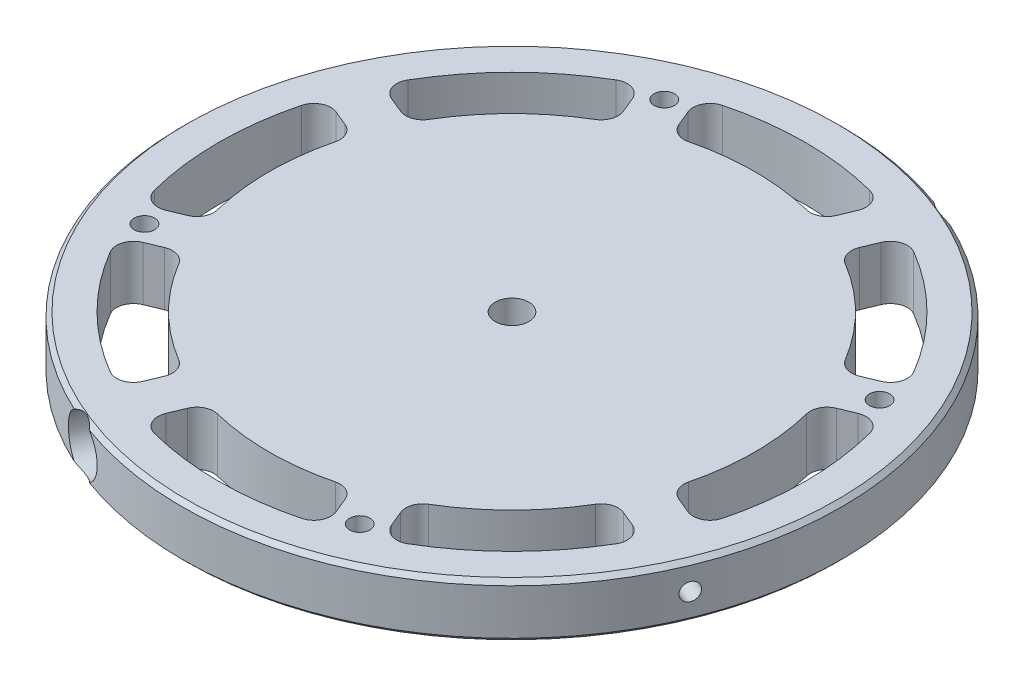
SolidWorks part; units mm, degrees
material "6061-T6 (SS)"
ref_plane "Front Plane" through (0, 0, 0) normal (0, 0, 1) x (1, 0, 0)
ref_plane "Top Plane" through (0, 0, 0) normal (0, 1, 0) x (1, 0, 0)
ref_plane "Right Plane" through (0, 0, 0) normal (1, 0, 0) x (0, 0, -1)
sketch "Sketch2" plane through (0, 0, 0) normal (1, 0, 0) x (0, 0, -1)
  line L0 (0, 0) -> (-77.55, 0)
  line L1 (-77.55, 0) -> (-77.55, 12.7)
  line L2 (-77.55, 12.7) -> (0, 12.7)
  line L5 (0, 12.7) -> (0, 0)
  dimension "D1" = 77.55
  dimension "D2" = 12.7
ref_axis "Axis1" through (0, -0.8888, 0) along (0, 1, 0)
revolve "Revolve1" add sketch "Sketch2" angle 360 about axis through (0, -0.8888, 0) along (0, 1, 0)
hole_wizard "#12 (0.189) Diameter Hole1" positions "Sketch6" profile "Sketch7" hole size "#12" standard "ANSI Inch" end condition through all
sketch "Sketch6" plane through (0, 12.7, 0) normal (0, 1, 0) x (1, 0, 0)
  line L0 (0, 0) -> (-53.438, 129.0108) construction
  line L2 (0, 0) -> (0, 109.0908) construction
  point P0 (-25.3336, 61.1608)
  dimension "D1" = 22.5
  dimension "D2" = 66.2
sketch "Sketch7" plane through (-25.3336, 12.7, -61.1608) normal (1, 0, 0) x (0, 0, 1)
  line L0 (0, 0) -> (0, 12.7)
  line L1 (0, 12.7) -> (2.4003, 12.7)
  line L2 (2.4003, 12.7) -> (2.4003, 0)
  line L5 (2.4003, 0) -> (0, 0)
  line L11 (0, -6.35) -> (0, 107.95) construction
  dimension "Thru Hole Dia." = 4.8006
  dimension "Thru Hole Depth" = 12.7
pattern_circular "CirPattern3" count 4 over 360 about axis through (0, 0, 0) along (0, 1, 0) of "#12 (0.189) Diameter Hole1"
sketch "Sketch8" plane through (0, 12.7, 0) normal (0, 1, 0) x (1, 0, 0)
  line L4 (0, 0) -> (0, 93.9995) construction
  line L5 (0, 0) -> (113.8372, 0) construction
  line L6 (-17.1671, 54.5107) -> (-21.7355, 65.5398)
  line L7 (17.1671, 54.5107) -> (21.7355, 65.5398)
  line L8 (0, 0) -> (-25.3336, 61.1608) construction
  arc A0 (-17.1671, 54.5107) -> (17.1671, 54.5107) centre (0, 0) cw
  arc A1 (-21.7355, 65.5398) -> (21.7355, 65.5398) centre (0, 0) cw
  circle A2 centre (0, 0) radius 77.55 construction
  dimension "D1" = 57.15
  dimension "D2" = 8.5
  dimension "D3" = 5
extrude "Cut-Extrude1" cut sketch "Sketch8" against normal through all
fillet "Fillet1" radius 4 4 edges at (17.1671, 6.35, -54.5107) (21.7355, 6.35, -65.5398) (-17.1671, 6.35, -54.5107) (-21.7355, 6.35, -65.5398)
pattern_circular "CirPattern4" count 8 over 360 about axis through (0, 0, 0) along (0, 1, 0) of "Cut-Extrude1", "Fillet1"
chamfer "Chamfer1" distance 1 angle 45 2 edges at (0, 0, -77.55) (0, 12.7, -77.55)
ref_plane "Plane1" through (0, 0, 0) normal (0.9239, 0, 0.3827) x (0, 1, 0)
hole_wizard "#20 (0.161) Diameter Hole1" positions "Sketch16" profile "Sketch15" hole size "#20" standard "ANSI Inch"
sketch "Sketch16" plane through (0, 0, 0) normal (0.9239, 0, 0.3827) x (0, 1, 0)
  point P0 (6.35, 0)
  dimension "D1" = 6.35
sketch "Sketch15" plane through (0, 6.35, 0) normal (0, 1, 0) x (-0.3827, 0, 0.9239)
  line L0 (0, 0) -> (0, 101.324)
  line L1 (0, 101.324) -> (2.0447, 101.324)
  line L2 (2.0447, 101.324) -> (2.0447, 0)
  line L5 (2.0447, 0) -> (0, 0)
  line L11 (0, -6.35) -> (0, 107.95) construction
  dimension "Thru Hole Dia." = 4.0894
  dimension "Thru Hole Depth" = 101.324
ref_plane "Plane2" through (29.6771, 0, -71.6469) normal (0.3827, 0, -0.9239) x (-0.9239, 0, -0.3827)
sketch "Sketch19" plane through (29.6771, 0, -71.6469) normal (0.3827, 0, -0.9239) x (-0.9239, 0, -0.3827)
  line L0 (-76.55, 0) -> (76.55, 0) construction
  line L2 (0, -0.8888) -> (0, 13.5888) construction
  circle A0 centre (0, 6.35) radius 5.5625 construction
  circle A1 centre (0, 6.35) radius 6.25
  dimension "D1" = 12.5
  dimension "D2" = 6.35
extrude "Cut-Extrude3" cut sketch "Sketch19" against normal blind 5
pattern_circular "CirPattern5" count 2 over 360 about axis through (0, -0.8888, 0) along (0, 1, 0) of "Cut-Extrude3"
hole_wizard "#10-24 Tapped Hole1" positions "Sketch20" profile "Sketch21" tap size "#10-24" standard "ANSI Inch"
sketch "Sketch20" plane through (-27.7637, 0, 67.0275) normal (-0.3827, 0, 0.9239) x (0.9239, 0, 0.3827)
  circle A0 centre (0, 6.35) radius 6.25
  circle A1 centre (0, 6.35) radius 6.25 construction
  point P0 (0, 6.35)
sketch "Sketch21" plane through (-27.7637, 6.35, 67.0275) normal (0, 1, 0) x (0.9239, 0, 0.3827)
  line L0 (0, 0) -> (0, 51.9408)
  line L1 (0, 51.9408) -> (1.8986, 50.8)
  line L2 (1.8986, 50.8) -> (1.8986, 0)
  line L5 (1.8986, 0) -> (0, 0)
  line L10 (0, 51.9408) -> (-1.8986, 50.8) construction
  line L11 (0, -6.35) -> (0, 107.95) construction
  dimension "Tap Drill Dia." = 3.7973
  dimension "Tap Drill Depth" = 50.8
  dimension "Drill Angle" = 118
pattern_circular "CirPattern6" count 2 over 360 about axis through (0, -0.8888, 0) along (0, 1, 0) of "#10-24 Tapped Hole1"
sketch "Sketch22" plane through (0, 12.7, 0) normal (0, 1, 0) x (1, 0, 0)
  circle A0 centre (0, 0) radius 3.9688
  dimension "D1" = 7.9375
extrude "Cut-Extrude4" cut sketch "Sketch22" against normal blind 12.8
equation "\"TubeDiameter\" = 6.500in"
equation "\"D1@Sketch2\"=(\"TubeDiameter\"/2)-5mm"
equation "\"D2@Sketch6\"=66.2"
